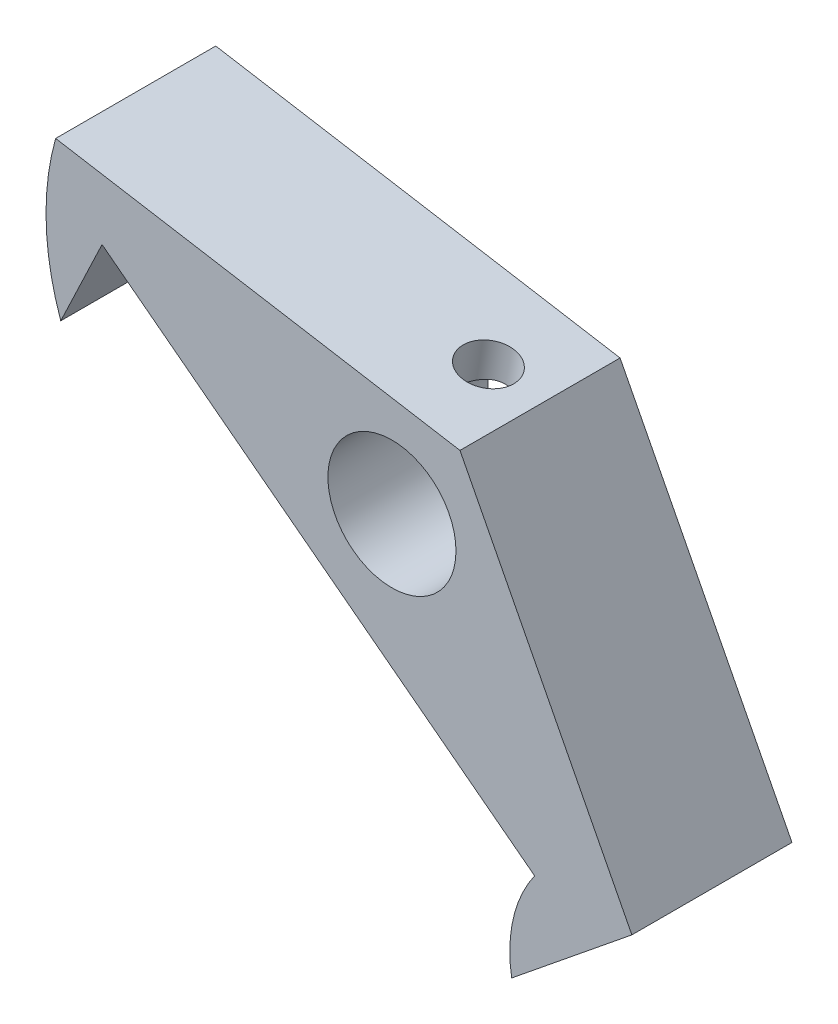
SolidWorks part; units mm, degrees
ref_plane "Front Plane" through (0, 0, 0) normal (0, 0, 1) x (1, 0, 0)
ref_plane "Top Plane" through (0, 0, 0) normal (0, 1, 0) x (1, 0, 0)
ref_plane "Right Plane" through (0, 0, 0) normal (1, 0, 0) x (0, 0, -1)
sketch "Sketch1" plane through (0, 0, 0) normal (0, 0, 1) x (1, 0, 0)
  line L6 (7.493, 88.3594) -> (2.1246, 98.7793)
  line L7 (2.1246, 98.7793) -> (-10.5024, 100.9027)
  line L8 (-10.3424, 96.0498) -> (-9.0532, 98.7587)
  line L9 (-9.0532, 98.7587) -> (4.4566, 88.4387)
  line L10 (3.7395, 85.3172) -> (6.0701, 87.2062)
  line L11 (6.0701, 87.2062) -> (7.493, 88.3594)
  line L12 (7.493, 88.3594) -> (2.1246, 98.7793)
  line L13 (2.1246, 98.7793) -> (-10.5024, 100.9027)
  line L14 (-10.3424, 96.0498) -> (-9.0532, 98.7587)
  line L15 (-9.0532, 98.7587) -> (4.4566, 88.4387)
  line L16 (3.7395, 85.3172) -> (6.0701, 87.2062)
  line L17 (6.0701, 87.2062) -> (7.493, 88.3594)
  arc A2 (-10.5024, 100.9027) -> (-10.3424, 96.0498) centre (-2.7854, 98.7281) ccw
  arc A3 (4.4566, 88.4387) -> (3.7395, 85.3172) centre (7.8628, 86.013) ccw
  arc A4 (-10.5024, 100.9027) -> (-10.3424, 96.0498) centre (-2.7854, 98.7281) ccw
  arc A5 (4.4566, 88.4387) -> (3.7395, 85.3172) centre (7.8628, 86.013) ccw
  circle A8 centre (0, 95.9979) radius 2 construction
  circle A9 centre (0, 95.9979) radius 2
  dimension "D1" = 0
extrude "Boss-Extrude1" add sketch "Sketch1" along normal up to vertex (5 mm away)
hole_wizard "M2x0.4 Tapped Hole1" positions "Sketch2" profile "Sketch3" tap size "M2x0.4" standard "ANSI Metric"
sketch "Sketch2" plane through (16.2127, 96.4102, 0) normal (0.1658, 0.9862, 0) x (0.9862, -0.1658, 0)
  line L1 (-17.9198, -5) -> (-13.9198, -5) construction
  line L2 (-17.9198, -5) -> (-13.9198, -5)
  line L3 (-14.2858, -5) -> (-14.2858, 0) construction
  line L4 (-14.2858, -5) -> (-14.2858, 0)
  point P0 (-15.9198, -2.5)
  point P8 (-16.2766, -2.0082)
  point P11 (-14.2858, -2.5)
  point P12 (-15.9198, -5)
sketch "Sketch3" plane through (0.5133, 99.0502, 2.5) normal (0, 0, 1) x (-0.9862, 0.1658, 0)
  line L0 (0, 0) -> (0, 3.4807)
  line L1 (0, 3.4807) -> (0.8, 3)
  line L2 (0.8, 3) -> (0.8, 0)
  line L5 (0.8, 0) -> (0, 0)
  line L10 (0, 3.4807) -> (-0.8, 3) construction
  line L11 (0, -6.35) -> (0, 107.95) construction
  dimension "Tap Drill Dia." = 1.6
  dimension "Tap Drill Depth" = 3
  dimension "Drill Angle" = 118
cosmetic thread "Hole Thread1" parameters "D1"=1.2621, "D2"=2
